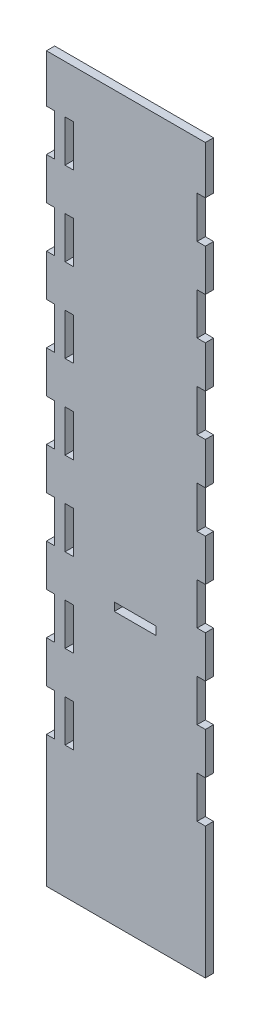
SolidWorks part; units mm, degrees
material "Acrylic (Medium-high impact)"
ref_plane "Front Plane" through (0, 0, 0) normal (0, 0, 1) x (1, 0, 0)
ref_plane "Top Plane" through (0, 0, 0) normal (0, 1, 0) x (1, 0, 0)
ref_plane "Right Plane" through (0, 0, 0) normal (1, 0, 0) x (0, 0, -1)
sketch "Sketch1" plane through (0, 0, 0) normal (0, 0, 1) x (1, 0, 0)
  line L89 (-3.175, 50.8) -> (-3.175, 34.64)
  line L90 (0, 0) -> (-3.175, 0)
  line L92 (-3.175, 50.8) -> (0, 50.8)
  line L97 (0, 279.4) -> (-3.175, 279.4)
  line L98 (0, 50.8) -> (-3.175, 50.8)
  line L99 (-3.175, 83.12) -> (-3.175, 66.96)
  line L100 (-3.175, 66.9636) -> (0, 66.9636)
  line L101 (0, 66.9636) -> (0, 50.8)
  line L114 (-3.175, 66.9636) -> (0, 66.9636)
  line L149 (58.175, 34.64) -> (58.175, 0)
  line L150 (-3.175, 83.12) -> (0, 83.12)
  line L198 (0, 99.2836) -> (0, 83.12)
  line L199 (-3.175, 99.2836) -> (0, 99.2836)
  line L201 (-3.175, 115.44) -> (-3.175, 99.28)
  line L241 (-3.175, 115.44) -> (0, 115.44)
  line L243 (0, 131.6036) -> (0, 115.44)
  line L244 (-3.175, 131.6036) -> (0, 131.6036)
  line L245 (-3.175, 147.76) -> (-3.175, 131.6)
  line L246 (-3.175, 147.76) -> (0, 147.76)
  line L247 (0, 163.9236) -> (0, 147.76)
  line L248 (-3.175, 163.9236) -> (0, 163.9236)
  line L249 (-3.175, 180.08) -> (-3.175, 163.92)
  line L250 (-3.175, 180.08) -> (0, 180.08)
  line L251 (0, 196.2436) -> (0, 180.08)
  line L252 (-3.175, 196.2436) -> (0, 196.2436)
  line L253 (-3.175, 212.4) -> (-3.175, 196.24)
  line L254 (-3.175, 212.4) -> (0, 212.4)
  line L255 (0, 228.5636) -> (0, 212.4)
  line L256 (-3.175, 228.5636) -> (0, 228.5636)
  line L257 (-3.175, 244.72) -> (-3.175, 228.56)
  line L258 (-3.175, 244.72) -> (0, 244.72)
  line L259 (0, 260.8836) -> (0, 244.72)
  line L260 (-3.175, 260.8836) -> (0, 260.8836)
  line L261 (-3.175, 260.8836) -> (-3.175, 279.4)
  line L262 (0, 279.4) -> (55, 279.4)
  line L263 (-3.175, 34.64) -> (-3.175, 0)
  line L264 (58.175, 260.8836) -> (58.175, 279.4)
  line L265 (0, 0) -> (55, 0)
  line L266 (58.175, 260.8836) -> (55, 260.8836)
  line L267 (55, 260.8836) -> (55, 244.72)
  line L268 (58.175, 244.72) -> (55, 244.72)
  line L269 (58.175, 244.72) -> (58.175, 228.56)
  line L270 (58.175, 228.5636) -> (55, 228.5636)
  line L271 (55, 228.5636) -> (55, 212.4)
  line L272 (58.175, 212.4) -> (55, 212.4)
  line L273 (58.175, 212.4) -> (58.175, 196.24)
  line L274 (58.175, 196.2436) -> (55, 196.2436)
  line L275 (-3.175, 228.6) -> (0, 228.6) [skipped]
  line L276 (-3.175, 212.4364) -> (0, 212.4364) [skipped]
  line L277 (-3.175, 212.4364) -> (0, 212.4364) [skipped]
  line L278 (0, 212.4364) -> (0, 196.2727) [skipped]
  line L279 (0, 228.6) -> (0, 212.4364) [skipped]
  line L280 (55, 196.2436) -> (55, 180.08)
  line L281 (58.175, 180.08) -> (55, 180.08)
  line L282 (-3.175, 196.2727) -> (0, 196.2727) [skipped]
  line L283 (-3.175, 196.2727) -> (0, 196.2727) [skipped]
  line L284 (0, 196.2727) -> (0, 180.1091) [skipped]
  line L285 (58.175, 180.08) -> (58.175, 163.92)
  line L286 (58.175, 163.9236) -> (55, 163.9236)
  line L287 (0, 180.1091) -> (0, 163.9455) [skipped]
  line L288 (0, 163.9455) -> (0, 147.7818) [skipped]
  line L289 (-3.175, 180.1091) -> (0, 180.1091) [skipped]
  line L290 (55, 163.9236) -> (55, 147.76)
  line L291 (-3.175, 163.9455) -> (0, 163.9455) [skipped]
  line L292 (-3.175, 163.9455) -> (0, 163.9455) [skipped]
  line L293 (0, 83.1273) -> (0, 66.9636) [skipped]
  line L294 (58.175, 147.76) -> (55, 147.76)
  line L295 (58.175, 147.76) -> (58.175, 131.6)
  line L296 (0, 99.2909) -> (0, 83.1273) [skipped]
  line L297 (-3.175, 83.1273) -> (0, 83.1273) [skipped]
  line L298 (-3.175, 83.1273) -> (0, 83.1273) [skipped]
  line L299 (-3.175, 99.2909) -> (0, 99.2909) [skipped]
  line L300 (-3.175, 99.2909) -> (0, 99.2909) [skipped]
  line L301 (-3.175, 115.4545) -> (0, 115.4545) [skipped]
  line L302 (-3.175, 115.4545) -> (0, 115.4545) [skipped]
  line L303 (-3.175, 131.6182) -> (0, 131.6182) [skipped]
  line L304 (-3.175, 131.6182) -> (0, 131.6182) [skipped]
  line L305 (-3.175, 147.7818) -> (0, 147.7818) [skipped]
  line L306 (-3.175, 147.7818) -> (0, 147.7818) [skipped]
  line L307 (58.175, 131.6036) -> (55, 131.6036)
  line L308 (0, 147.7818) -> (0, 131.6182) [skipped]
  line L309 (0, 131.6182) -> (0, 115.4545) [skipped]
  line L310 (55, 131.6036) -> (55, 115.44)
  line L312 (0, 115.4545) -> (0, 99.2909) [skipped]
  line L313 (0, 180.1091) -> (1.0458, 180.1091) [skipped]
  line L315 (58.175, 115.44) -> (55, 115.44)
  line L316 (58.175, 115.44) -> (58.175, 99.28)
  line L317 (58.175, 99.2836) -> (55, 99.2836)
  line L325 (55, 99.2836) -> (55, 83.12)
  line L329 (55, 0) -> (58.175, 0)
  line L330 (58.175, 83.12) -> (55, 83.12)
  line L332 (58.175, 66.9636) -> (55, 66.9636)
  line L334 (55, 66.9636) -> (55, 50.8)
  line L335 (58.175, 66.9636) -> (55, 66.9636)
  line L336 (58.175, 83.12) -> (58.175, 66.96)
  line L337 (55, 50.8) -> (58.175, 50.8)
  line L338 (55, 279.4) -> (58.175, 279.4)
  line L339 (58.175, 50.8) -> (55, 50.8)
  line L340 (58.175, 50.8) -> (58.175, 34.64)
  dimension "D1" = 279.4
  dimension "D3" = 50.8
  dimension "D4" = 3.175
  dimension "D5" = 16.1636
  dimension "D2" = 55
  dimension "D7" = 3.175
  dimension "D9" = 16.16
  dimension "D10" = 34.64
  dimension "D11" = 55
  dimension "D12" = 3.175
  dimension "D6" = 11
  dimension "D8" = 7
extrude "Boss-Extrude1" add sketch "Sketch1" along normal blind 3.175
sketch "Sketch3" plane through (0, 0, 3.175) normal (0, 0, 1) x (1, 0, 0)
  line L0 (0, 66.9636) -> (0, 50.8) construction
  line L3 (4, 66.9636) -> (7.175, 66.9636)
  line L4 (4, 66.9636) -> (4, 50.8)
  line L5 (4, 50.8) -> (7.175, 50.8)
  line L6 (7.175, 66.9636) -> (7.175, 50.8)
  line L7 (4, 99.2836) -> (4, 83.12)
  line L8 (4, 99.2836) -> (7.175, 99.2836)
  line L9 (7.175, 99.2836) -> (7.175, 83.12)
  line L10 (4, 83.12) -> (7.175, 83.12)
  line L11 (4, 131.6036) -> (4, 115.44)
  line L12 (4, 131.6036) -> (7.175, 131.6036)
  line L29 (7.175, 131.6036) -> (7.175, 115.44)
  line L32 (4, 115.44) -> (7.175, 115.44)
  line L35 (4, 163.9236) -> (4, 147.76)
  line L38 (4, 163.9236) -> (7.175, 163.9236)
  line L41 (7.175, 163.9236) -> (7.175, 147.76)
  line L43 (4, 147.76) -> (7.175, 147.76)
  line L44 (4, 196.2436) -> (4, 180.08)
  line L45 (4, 196.2436) -> (7.175, 196.2436)
  line L46 (7.175, 196.2436) -> (7.175, 180.08)
  line L47 (4, 180.08) -> (7.175, 180.08)
  line L48 (4, 228.5636) -> (4, 212.4)
  line L49 (4, 228.5636) -> (7.175, 228.5636)
  line L50 (7.175, 228.5636) -> (7.175, 212.4)
  line L51 (4, 212.4) -> (7.175, 212.4)
  line L52 (4, 260.8836) -> (4, 244.72)
  line L53 (4, 260.8836) -> (7.175, 260.8836)
  line L54 (7.175, 260.8836) -> (7.175, 244.72)
  line L55 (4, 244.72) -> (7.175, 244.72)
  dimension "D1" = 7
  dimension "D2" = 3.175
  dimension "D3" = 4
extrude "Cut-Extrude2" cut sketch "Sketch3" against normal blind 10
sketch "Sketch4" plane through (0, 0, 3.175) normal (0, 0, 1) x (1, 0, 0)
  line L0 (58.175, 0) -> (-3.175, 0) construction
  line L1 (23.0075, 108.175) -> (39.1675, 108.175)
  line L2 (23.0075, 108.175) -> (23.0075, 105)
  line L3 (23.0075, 105) -> (39.1675, 105)
  line L4 (39.1675, 108.175) -> (39.1675, 105)
  line L5 (7.175, 115.44) -> (55, 115.44) construction
  line L7 (31.0875, 108.175) -> (31.0875, 105) construction
  point P12 (31.0875, 115.44)
  dimension "D1" = 16.16
  dimension "D2" = 3.175
  dimension "D3" = 105
  dimension "D4" = 0
extrude "Cut-Extrude3" cut sketch "Sketch4" against normal blind 10
equation "\"D7@Sketch1\"=\"D5@Sketch1\""
equation "\"D8@Sketch1\"=\"D3@Sketch1\""
equation "\"D10@Sketch1\"=((\"D1@Sketch1\"-2*\"D8@Sketch1\")/(\"D6@Sketch1\"))"
equation "\"D9@Sketch2\"=\"D3@Sketch2\""
equation "\"D12@Sketch1\"=\"D10@Sketch1\""
equation "\"D8@Sketch2\"=\"D4@Sketch2\""
equation "\"D10@Sketch2\"=\"D5@Sketch2\""
equation "\"D9@Sketch1\"=\"D3@Sketch1\""
equation "\"D5@Sketch1\"=((\"D1@Sketch1\"-2*\"D3@Sketch1\")/(\"D6@Sketch1\"))"
